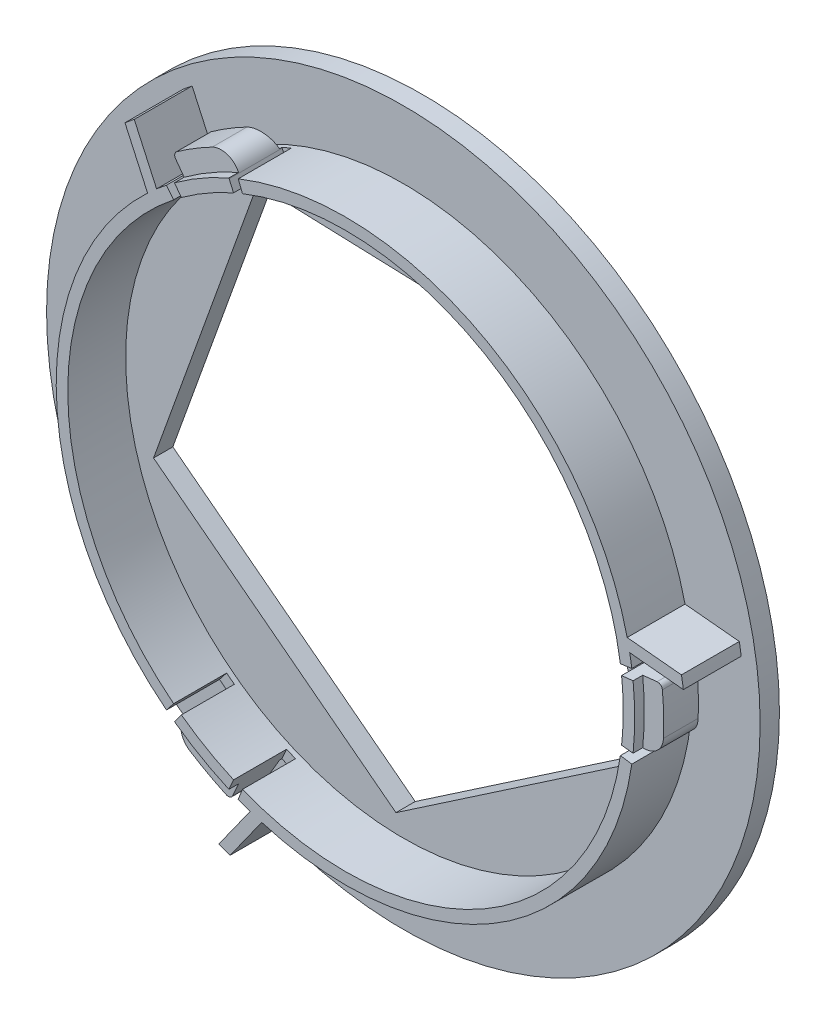
SolidWorks part; units mm, degrees
ref_plane "Front Plane" through (0, 0, 0) normal (0, 0, 1) x (1, 0, 0)
ref_plane "Top Plane" through (0, 0, 0) normal (0, 1, 0) x (1, 0, 0)
ref_plane "Right Plane" through (0, 0, 0) normal (1, 0, 0) x (0, 0, -1)
sketch "Sketch3" plane through (0, 0, 0) normal (0, 0, 1) x (1, 0, 0)
  line L0 (-0.0094, -0.2999) -> (16.3893, 20.8479) construction
  line L1 (15.3668, 19.5292) -> (-14.1164, 20.4513)
  line L2 (-14.1164, 20.4513) -> (-24.1042, -7.304)
  line L3 (-24.1042, -7.304) -> (-0.7937, -25.3798)
  line L4 (-0.7937, -25.3798) -> (23.6007, -8.796)
  line L5 (-0.0094, -0.2999) -> (29.9069, -0.2999) construction
  line L6 (-0.0094, -0.2999) -> (25.1708, -9.361) construction
  line L10 (-0.6657, -26.9251) -> (25.1708, -9.361)
  line L11 (25.1708, -9.361) -> (16.3893, 20.8479)
  line L12 (16.3893, 20.8479) -> (-14.7759, 21.6152)
  line L13 (-14.7759, 21.6152) -> (-25.354, -7.7808)
  line L14 (-25.354, -7.7808) -> (-0.6657, -26.9251)
  line L15 (23.6007, -8.796) -> (15.3668, 19.5292)
  circle A0 centre (-0.0094, -0.2999) radius 20.3 construction
  dimension "D2" = 40.6
sketch "Sketch55" plane through (0, 0, 0) normal (0, 0, 1) x (1, 0, 0)
  line L5 (-15.1311, 22.3353) -> (-25.905, -7.6046)
  line L6 (-25.905, -7.6046) -> (-0.7697, -26.8838)
  line L7 (-0.7697, -26.8838) -> (25.3546, -9.1239)
  line L8 (25.3546, -9.1239) -> (16.5274, 21.2424)
  line L9 (16.5274, 21.2424) -> (-15.1311, 22.3353)
  circle A0 centre (0, 0) radius 37
  circle A1 centre (0, 0) radius 21.8 construction
  point P3 (0, -37)
  dimension "D1" = 37
  dimension "D2" = 43.6
extrude "Boss-Extrude17" add sketch "Sketch55" against normal blind 8
sketch "Sketch56" plane through (0, 0, 0) normal (0, 0, 1) x (1, 0, 0)
  circle A1 centre (0, 0) radius 30
  circle A2 centre (0, 0) radius 37 construction
  circle A3 centre (0, 0) radius 37
  circle A4 centre (0, 0) radius 28.8
  circle M1 centre (0, 0) radius 37
  dimension "D1" = 60
  dimension "D2" = 1.2
extrude "Cut-Extrude20" cut sketch "Sketch56" against normal offset from surface (6 mm away) 2 contours A1 M1 | A4 up to face at (0.0152, -0.0069, -8)
ref_plane "Plane9" through (0, 0, -1) normal (0, 0, 1) x (1, 0, 0)
sketch "Sketch58" plane through (0, 0, -1) normal (0, 0, 1) x (1, 0, 0)
  line L0 (0, 0) -> (52.2478, 0) construction
  line L1 (32.0595, 3.5) -> (27.9317, 3.5) construction
  line L2 (32.0595, -3.5) -> (27.9317, -3.5) construction
  line L3 (27.9317, -3.5) -> (27.9317, 3.5) construction
  circle A2 centre (0, 0) radius 32.25
  arc A4 (32.0595, -3.5) -> (32.0595, 3.5) centre (0, 0) ccw
  point P0 (32.0595, 3.5)
  point P3 (32.0595, -3.5)
  point P6 (32, 0)
  dimension "D2" = 3.5
  dimension "D1" = 2.25
sketch "Sketch59" plane through (0, 0, 0) normal (0, 1, 0) x (1, 0, 0)
  line L0 (32, 1) -> (32, 4.6)
  line L1 (30, 5.25) -> (30, 1)
  line L2 (30, 0) -> (30, 6) construction
  line L3 (0, 1) -> (52.2478, 1) construction
  line L4 (30, 1) -> (32, 1)
  line L6 (30, 5.25) -> (32, 4.6)
  dimension "D1" = 3.6
  dimension "D2" = 4.25
sweep "Sweep1" add profiles "Sketch59" path "Sketch58"
sketch "Sketch60" plane through (0, 0, 0) normal (0, 0, 1) x (1, 0, 0)
  line L0 (0, 0) -> (31.811, 3.4729) construction
  line L1 (0, 0) -> (31.811, -3.4729) construction
  line L3 (0, 0) -> (32, 0) construction
  line L4 (0, 0) -> (38.7281, -5.6018) construction
  line L5 (0, 0) -> (38.7281, 5.6018) construction
  line L6 (29.691, 4.2946) -> (28.5034, 4.1228)
  line L7 (29.8228, 3.2558) -> (28.6299, 3.1256)
  line L8 (29.8228, -3.2558) -> (28.6299, -3.1256)
  line L9 (29.691, -4.2946) -> (28.5034, -4.1228)
  circle A1 centre (0, 0) radius 30 construction
  circle A3 centre (0, 0) radius 28.8 construction
  arc A4 (28.5034, -4.1228) -> (28.6299, -3.1256) centre (0, 0) ccw
  arc A5 (28.6299, 3.1256) -> (28.5034, 4.1228) centre (0, 0) ccw
  arc A7 (31.811, -3.4729) -> (31.811, 3.4729) centre (0, 0) ccw construction
  arc A9 (29.8228, 3.2558) -> (29.691, 4.2946) centre (0, 0) ccw
  arc A10 (29.691, -4.2946) -> (29.8228, -3.2558) centre (0, 0) ccw
  dimension "D1" = 2
extrude "Cut-Extrude21" cut sketch "Sketch60" against normal offset from surface (5.5 mm away) 0.5 up to face at (37, 0, -6)
fillet "Fillet1" radius 0.5 1 edges at (31.811, 3.4729, -2.8)
fillet "Fillet2" radius 2 1 edges at (31.811, -3.4729, -2.8)
sketch "Sketch62" plane through (0, 0, -6) normal (0, 0, 1) x (1, 0, 0)
  line L0 (28.5034, 4.1228) -> (29.691, 4.2946) construction
  line L1 (28.5034, 4.1228) -> (29.691, 4.2946) construction
  line L2 (35.0354, 5.0677) -> (28.2253, 5.725)
  line L3 (34.8363, 6.2925) -> (27.947, 6.9574)
  circle A1 centre (0, 0) radius 28.8 construction
  circle A2 centre (0, 0) radius 35.4
  arc A3 (35.0354, 5.0677) -> (34.8363, 6.2925) centre (0, 0) ccw
  arc A4 (28.2253, 5.725) -> (27.947, 6.9574) centre (0, 0) ccw
  dimension "D2" = 13.743
  dimension "D3" = 1.2
  dimension "D1" = 1.6
extrude "Boss-Extrude18" add sketch "Sketch62" along normal up to surface (6 mm away) up to face at (-0.1514, 0, 0)
pattern_circular "CirPattern1" count 3 over 360 about axis through (0, 0, 0) along (0, 0, 1) of "Boss-Extrude18", "Sweep1", "Cut-Extrude21", "Fillet2", "Fillet1"
